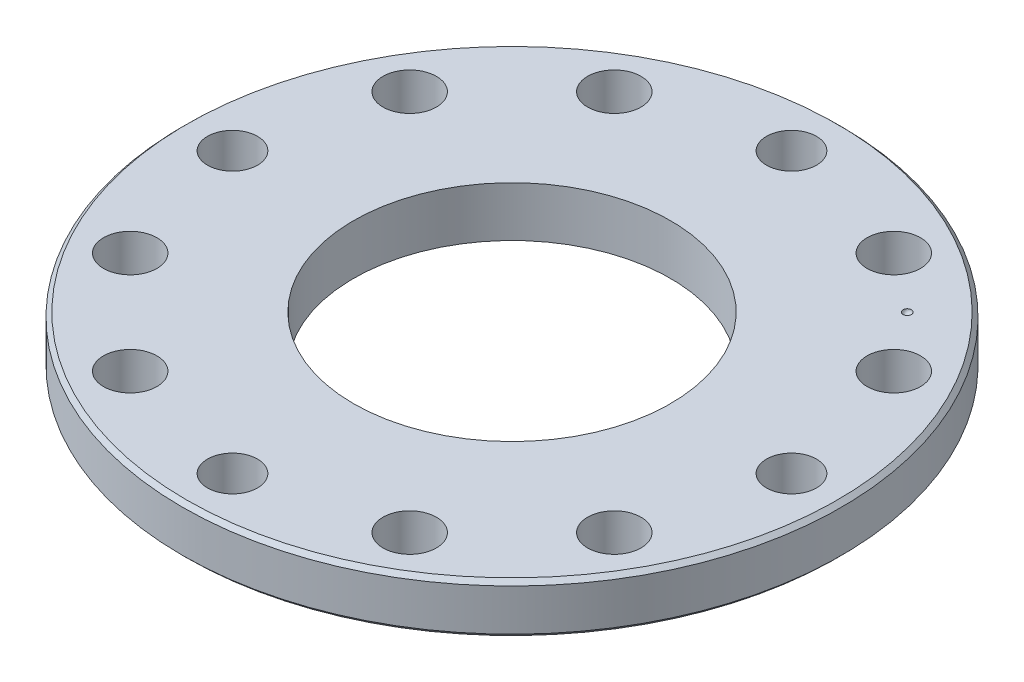
SolidWorks part; units mm, degrees
material " 09Г2С ГОСТ 4543-71"
ref_plane "Спереди" through (0, 0, 0) normal (0, 0, 1) x (1, 0, 0)
ref_plane "Сверху" through (0, 0, 0) normal (0, 1, 0) x (1, 0, 0)
ref_plane "Слева" through (0, 0, 0) normal (1, 0, 0) x (0, 0, -1)
sketch "Эскиз1" plane through (0, 0, 0) normal (0, 1, 0) x (1, 0, 0)
  line L1 (0, 33.5) -> (-16.75, 29.0119) construction
  line L2 (-16.75, 29.0119) -> (-29.0119, 16.75) construction
  line L3 (-29.0119, 16.75) -> (-33.5, 0) construction
  line L4 (-33.5, 0) -> (-29.0119, -16.75) construction
  line L5 (-29.0119, -16.75) -> (-16.75, -29.0119) construction
  line L6 (-16.75, -29.0119) -> (0, -33.5) construction
  line L7 (0, -33.5) -> (16.75, -29.0119) construction
  line L8 (16.75, -29.0119) -> (29.0119, -16.75) construction
  line L9 (29.0119, -16.75) -> (33.5, 0) construction
  line L10 (33.5, 0) -> (29.0119, 16.75) construction
  line L11 (29.0119, 16.75) -> (16.75, 29.0119) construction
  line L12 (16.75, 29.0119) -> (0, 33.5) construction
  circle A0 centre (0, 0) radius 19
  circle A1 centre (0, 0) radius 39.5
  circle A2 centre (0, 0) radius 33.5 construction
  circle A3 centre (0, 0) radius 33.5 construction
  circle A4 centre (0, 33.5) radius 3
  circle A5 centre (33.5, 0) radius 3
  circle A6 centre (-33.5, 0) radius 3
  circle A7 centre (0, -33.5) radius 3
  dimension "D1" = 6
  dimension "D2" = 79
  dimension "D3" = 38
  dimension "D4" = 6
extrude "Вытянуть1" add sketch "Эскиз1" against normal blind 6
hole_wizard "Отверстие с зазором M61" positions "Эскиз4" profile "Эскиз3" hole size "M6" standard "ГОСТ" end condition through all
sketch "Эскиз4" plane through (0, 0, 0) normal (0, 1, 0) x (-1, 0, 0)
  point P1 (16.75, 29.0119)
  point P4 (29.0119, -16.75)
  point P7 (-16.75, -29.0119)
  point P10 (-29.0119, 16.75)
  point P15 (16.75, -29.0119)
  point P18 (-29.0119, -16.75)
  point P21 (-16.75, 29.0119)
  point P24 (29.0119, 16.75)
sketch "Эскиз3" plane through (-16.75, 0, 29.0119) normal (1, 0, 0) x (0, 0, 1)
  line L0 (0, 0) -> (0, 6)
  line L1 (0, 6) -> (3.2, 6)
  line L2 (3.2, 6) -> (3.2, 0)
  line L5 (3.2, 0) -> (0, 0)
  line L11 (0, -6.35) -> (0, 107.95) construction
  dimension "Диаметр сквозного отверстия" = 6.4
  dimension "Глубина сквозного отверстия" = 6
chamfer "Фаска1" distance 0.5 angle 45 2 edges at (0, 0, 39.5) (0, -6, 39.5)
sketch "Эскиз5" plane through (0, 0, 0) normal (0, 1, 0) x (1, 0, 0)
  line L0 (26.4759, 26.4759) -> (0, 0) construction
  line L1 (0, 0) -> (0, -44.0609) construction
  line L2 (24.0416, 24.0416) -> (23.3345, 23.3345)
  arc A0 (24.0416, 24.0416) -> (23.3345, 23.3345) centre (23.6881, 23.6881) ccw
  circle A1 centre (0, 0) radius 33.5 construction
  dimension "D2" = 0.5
  dimension "D1" = 225
revolve "Вырез-Повернуть1" cut sketch "Эскиз5" angle 360 about L0
